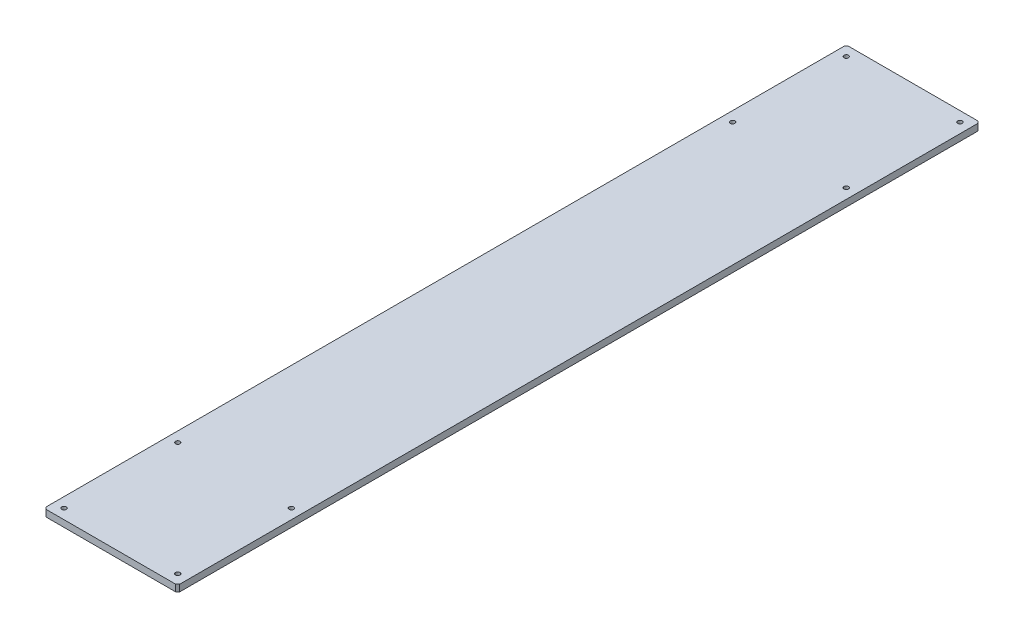
SolidWorks part; units mm, degrees
ref_plane "Front" through (0, 0, 0) normal (0, 0, 1) x (1, 0, 0)
ref_plane "Top" through (0, 0, 0) normal (0, 1, 0) x (1, 0, 0)
ref_plane "Right" through (0, 0, 0) normal (1, 0, 0) x (0, 0, -1)
sketch "Sketch1" plane through (0, 0, 0) normal (0, 1, 0) x (1, 0, 0)
  line L0 (100, 383.5792) -> (100, -384.7373) construction
  line L1 (-124.7429, 0) -> (226.6105, 0) construction
  line L3 (0, 600) -> (200, 600)
  line L4 (0, 600) -> (0, -600)
  line L5 (0, -600) -> (200, -600)
  line L6 (200, 600) -> (200, -600)
  dimension "D1" = 1200
  dimension "D2" = 200
extrude "Boss-Extrude1" add sketch "Sketch1" along normal blind 10
hole_wizard "M8x1.25 Tapped Hole1" positions "Sketch3" profile "Sketch2" tap size "M8x1.25" standard "JIS" end condition through all
sketch "Sketch3" plane through (0, 10, 0) normal (0, 1, 0) x (-1, 0, 0)
  line L0 (-247.1459, 0) -> (70.7619, 0) construction
  line L2 (-100, 575.5945) -> (-100, -419.5014) construction
  line L4 (-238.0628, 500) -> (41.696, 500) construction
  line L6 (-162.7033, -500) -> (101.6143, -500) construction
  line L8 (0, -600) -> (0, 600) construction
  point P0 (-15, -585)
  point P1 (-15, -415)
  point P3 (-185, -415)
  point P5 (-185, -585)
  point P7 (-185, 415)
  point P9 (-185, 585)
  point P11 (-15, 585)
  point P13 (-15, 415)
  dimension "D1" = 170
  dimension "D2" = 170
  dimension "D3" = 170
  dimension "D4" = 170
  dimension "D5" = 100
  dimension "D6" = 1000
sketch "Sketch2" plane through (15, 10, -585) normal (1, 0, 0) x (0, 0, 1)
  line L0 (0, 0) -> (0, 10)
  line L1 (0, 10) -> (3.4, 10)
  line L2 (3.4, 10) -> (3.4, 0)
  line L5 (3.4, 0) -> (0, 0)
  line L11 (0, -6.35) -> (0, 107.95) construction
  dimension "次ｻｰﾌｪｽまでのねじ下穴ﾄﾞﾘﾙ直径" = 6.8
  dimension "次ｻｰﾌｪｽまでのねじ下穴ﾄﾞﾘﾙの深さ" = 10
cosmetic thread "Hole Thread1" parameters "D2"=8
cosmetic thread "Hole Thread2" parameters "D2"=8
cosmetic thread "Hole Thread3" parameters "D2"=8
cosmetic thread "Hole Thread4" parameters "D2"=8
cosmetic thread "Hole Thread5" parameters "D2"=8
cosmetic thread "Hole Thread6" parameters "D2"=8
cosmetic thread "Hole Thread7" parameters "D2"=8
cosmetic thread "Hole Thread8" parameters "D2"=8
chamfer "Chamfer1" distance 3 angle 45 4 edges at (0, 5, 600) (200, 5, 600) (200, 5, -600) (0, 5, -600)
